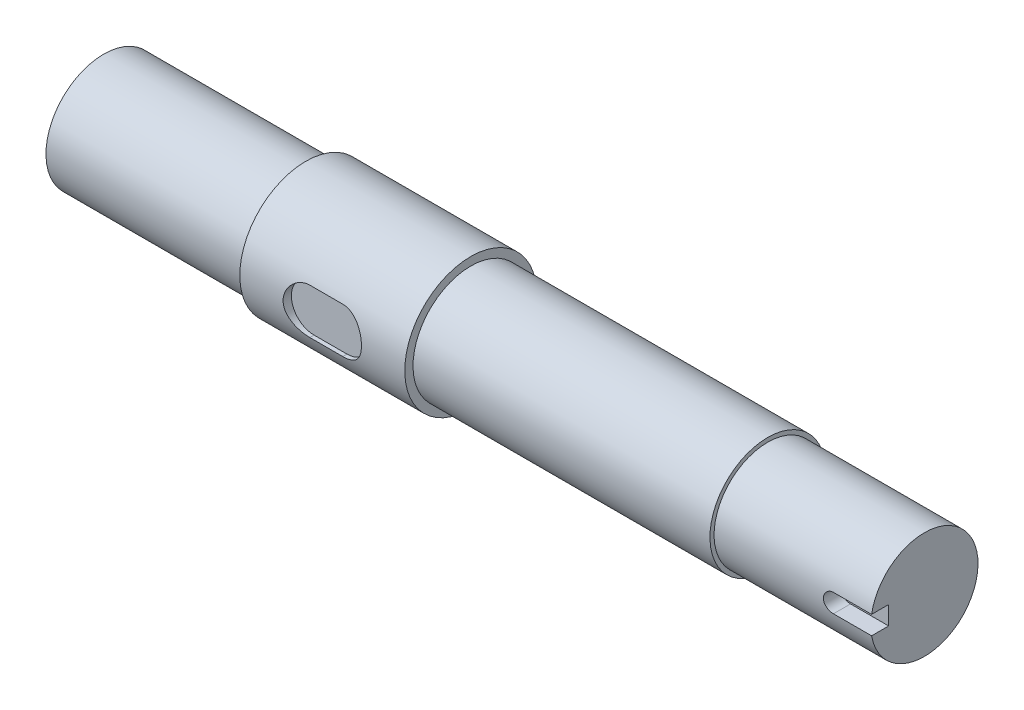
SolidWorks part; units mm, degrees
ref_plane "Front Plane" through (0, 0, 0) normal (0, 0, 1) x (1, 0, 0)
ref_plane "Top Plane" through (0, 0, 0) normal (0, 1, 0) x (1, 0, 0)
ref_plane "Right Plane" through (0, 0, 0) normal (1, 0, 0) x (0, 0, -1)
sketch "Sketch1" plane through (0, 0, 0) normal (0, 0, 1) x (1, 0, 0)
  line L0 (0, 0) -> (0, 21)
  line L1 (0, 21) -> (73.5, 21)
  line L2 (73.5, 21) -> (73.5, 24)
  line L3 (73.5, 24) -> (133.5, 24)
  line L4 (133.5, 24) -> (133.5, 21)
  line L5 (133.5, 21) -> (241.5, 21)
  line L6 (241.5, 21) -> (241.5, 19.5)
  line L7 (241.5, 19.5) -> (298.5, 19.5)
  line L8 (298.5, 19.5) -> (298.5, 0)
  line L9 (298.5, 0) -> (0, 0)
  point P8 (0, 0)
  point P12 (0, 0)
  point P13 (0, 0)
  point P14 (0, 0)
  point P15 (0, 0)
  point P16 (0, 0)
  point P17 (0, 0)
  point P18 (0, 0)
  point P19 (0, 0)
  point P20 (0, 0)
  point P21 (0, 0)
  dimension "D1" = 73.5
  dimension "D2" = 60
  dimension "D3" = 108
  dimension "D4" = 57
  dimension "D5" = 21
  dimension "D6" = 19.5
  dimension "D7" = 24
revolve "Revolve1" add sketch "Sketch1" angle 360 about L9
ref_plane "Plane1" through (0, 0, 19.5) normal (0, 0, 1) x (1, 0, 0)
sketch "Sketch3" plane through (0, 0, 19.5) normal (0, 0, 1) x (1, 0, 0)
  line L0 (312.375, 0) -> (284.625, 0) construction
  line L1 (298.5, -19.5) -> (298.5, 19.5) construction
  line L2 (312.375, -3.375) -> (284.625, -3.375)
  line L3 (312.375, 3.375) -> (284.625, 3.375)
  line L4 (241.5, 0) -> (298.5, 0) construction
  arc A0 (312.375, -3.375) -> (312.375, 3.375) centre (312.375, 0) ccw
  arc A1 (284.625, 3.375) -> (284.625, -3.375) centre (284.625, 0) ccw
  point P4 (298.5, 0)
  point P9 (0, 0)
  point P10 (0, 0)
  point P11 (0, 0)
  point P12 (0, 0)
  point P15 (288, 0)
  dimension "D1" = 10.5
  dimension "D2" = 6.75
extrude "Cut-Extrude1" cut sketch "Sketch3" against normal blind 6.5
ref_plane "Plane2" through (0, 0, 24) normal (0, 0, 1) x (1, 0, 0)
sketch "Sketch4" plane through (0, 0, 24) normal (0, 0, 1) x (1, 0, 0)
  line L0 (97.5, 0) -> (109.5, 0) construction
  line L1 (97.5, 8.25) -> (109.5, 8.25)
  line L2 (97.5, -8.25) -> (109.5, -8.25)
  line L3 (133.5, -21) -> (133.5, 21) construction
  arc A0 (97.5, 8.25) -> (97.5, -8.25) centre (97.5, 0) ccw
  arc A1 (109.5, -8.25) -> (109.5, 8.25) centre (109.5, 0) ccw
  point P3 (103.5, 0)
  dimension "D2" = 8.25
  dimension "D1" = 12
  dimension "D3" = 30
extrude "Cut-Extrude2" cut sketch "Sketch4" against normal blind 3
